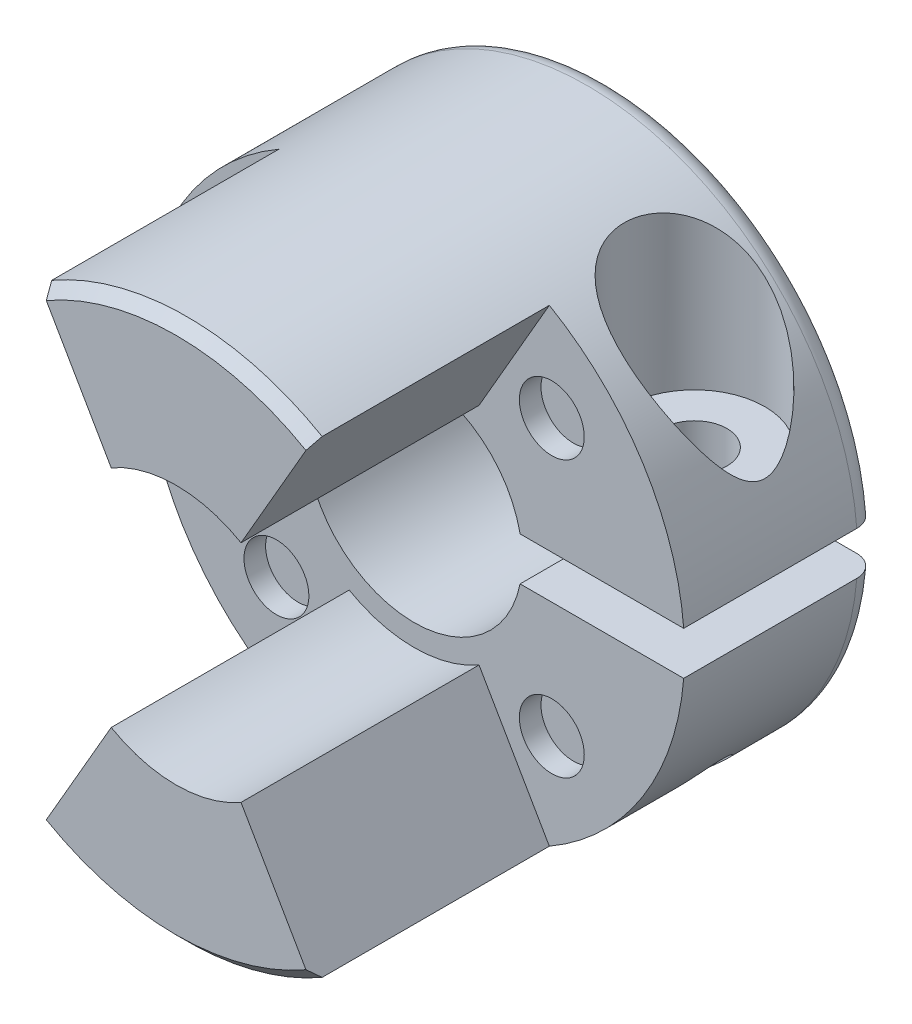
SolidWorks part; units mm, degrees
material "Liga 6061"
ref_plane "Plano frontal" through (0, 0, 0) normal (0, 0, 1) x (1, 0, 0)
ref_plane "Plano superior" through (0, 0, 0) normal (0, 1, 0) x (1, 0, 0)
ref_plane "Plano direito" through (0, 0, 0) normal (1, 0, 0) x (0, 0, -1)
sketch "Esboço1" plane through (0, 0, 0) normal (0, 0, 1) x (1, 0, 0)
  circle A0 centre (0, 0) radius 12.5
  dimension "D1" = 25
extrude "Ressalto-extrusão1" add sketch "Esboço1" along normal blind 20
sketch "Esboço2" plane through (0, 0, 20) normal (0, 0, 1) x (1, 0, 0)
  line L0 (0, 0) -> (0, 12.5) construction
  line L1 (0, 0) -> (6.25, 10.8253)
  line L2 (6.25, -10.8253) -> (0, 0)
  circle A0 centre (0, 0) radius 12.5 construction
  arc A2 (6.25, 10.8253) -> (6.25, -10.8253) centre (0, 0) cw
  dimension "D1" = 120
  dimension "D2" = 30
extrude "Corte-extrusão3" cut sketch "Esboço2" against normal blind 11
sketch "Esboço3" plane through (0, 0, 0) normal (0, 0, -1) x (-1, 0, 0)
  circle A0 centre (0, 0) radius 5
  dimension "D1" = 10
extrude "Corte-extrusão4" cut sketch "Esboço3" against normal through all
mirror "Espelhar1" about plane through (0, 0, 0) normal (1, 0, 0) of "Corte-extrusão3"
sketch "Esboço6" plane through (0, 0, 9) normal (0, 0, 1) x (1, 0, 0)
  line L1 (1, 1) -> (13, 1)
  line L2 (1, 1) -> (1, -1)
  line L3 (1, -1) -> (13, -1)
  line L4 (13, 1) -> (13, -1)
  line L5 (1, 1) -> (13, -1) construction
  line L6 (1, -1) -> (13, 1) construction
  point P0 (7, 0)
  dimension "D1" = 2
  dimension "D2" = 12
  dimension "D3" = 7
extrude "Corte-extrusão5" cut sketch "Esboço6" against normal through all
sketch "Esboço7" plane through (0, 1, 0) normal (0, -1, 0) x (1, 0, 0)
  line L0 (12.4599, 9) -> (12.4599, 0) construction
  circle A0 centre (8.4599, 4.5) radius 3.25
  point P4 (12.4599, 4.5)
  dimension "D1" = 6.5
  dimension "D2" = 4
extrude "Corte-extrusão6" cut sketch "Esboço7" against normal through all from offset 3 offset against normal yes
hole_wizard "Furo roscado de M3x0.51" positions "Esboço9" profile "Esboço8" tap size "M3x0.5" standard "Ansi Metric" end condition through all
sketch "Esboço9" plane through (0, 4, 0) normal (0, 1, 0) x (1, 0, 0)
  point P0 (8.4599, -4.5)
sketch "Esboço8" plane through (8.4599, 4, 4.5) normal (1, 0, 0) x (0, 0, 1)
  line L0 (0, 0) -> (0, 16.5)
  line L1 (0, 16.5) -> (1.25, 16.5)
  line L2 (1.25, 16.5) -> (1.25, 0)
  line L5 (1.25, 0) -> (0, 0)
  line L11 (0, -6.35) -> (0, 107.95) construction
  dimension "Thru Tap Drill Dia." = 2.5
  dimension "Thru Tap Drill Depth" = 16.5
cosmetic thread "Rosca de furo1" parameters "D2"=3
fillet "Filete1" radius 1 1 edges at (-12.5, 0, 0)
sketch "Esboço10" plane through (0, 0, 9) normal (0, 0, 1) x (1, 0, 0)
  line L0 (0, 0) -> (0, -3.9553) construction
  line L1 (6.364, -6.364) -> (0, 0) construction
  circle A0 centre (6.364, -6.364) radius 1.5
  dimension "D1" = 3
  dimension "D2" = 9
  dimension "D3" = 45
extrude "Corte-extrusão7" cut sketch "Esboço10" against normal blind 1
chamfer "Chanfro1" distance 0.5 angle 45 2 edges at (0, 12.5, 20) (0, -12.5, 20)
sketch "Esboço11" plane through (0, 4, 0) normal (0, 1, 0) x (1, 0, 0)
  circle A0 centre (8.4599, -4.5) radius 1.5
  dimension "D1" = 3
extrude "Corte-extrusão8" cut sketch "Esboço11" against normal up to next
sketch "Esboço12" plane through (0, 0, 20) normal (0, 0, 1) x (1, 0, 0)
  circle A0 centre (0, 0) radius 6
  dimension "D1" = 12
extrude "Corte-extrusão9" cut sketch "Esboço12" against normal up to surface (11 mm away) up to face at (-6.5625, 0, 9)
pattern_circular "PadrãoCircular1" count 4 over 360 about axis through (0, 0, 0) along (0, 0, 1) of "Corte-extrusão7"
chamfer "Chanfro2" distance 0.5 angle 45 1 edges at (-5, 0, 0)
